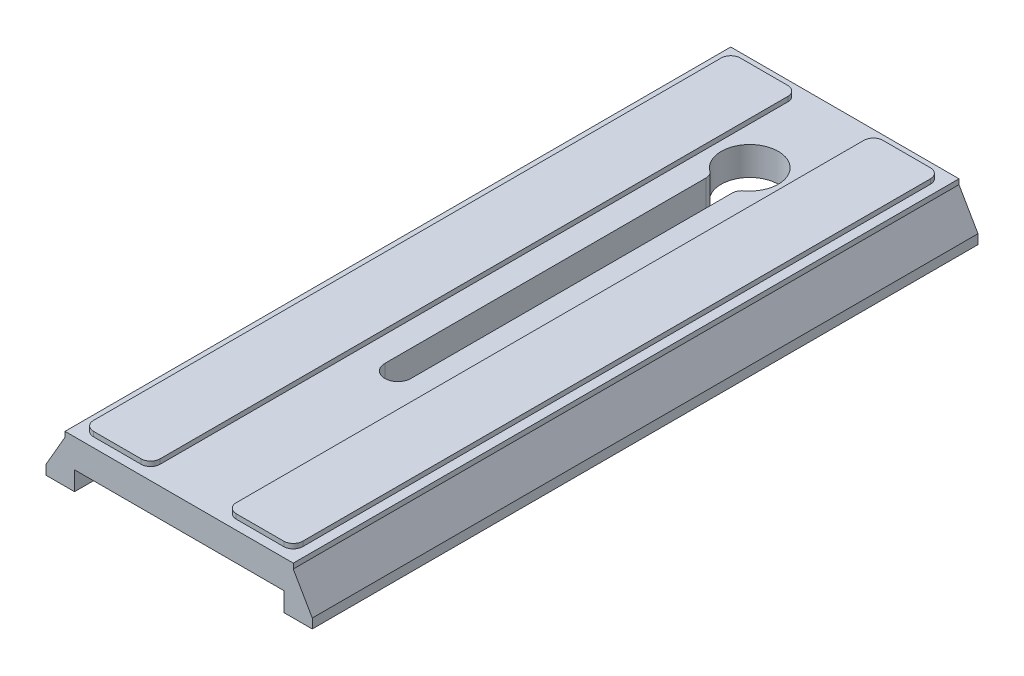
SolidWorks part; units mm, degrees
ref_plane "Спереди" through (0, 0, 0) normal (0, 0, 1) x (1, 0, 0)
ref_plane "Сверху" through (0, 0, 0) normal (0, 1, 0) x (1, 0, 0)
ref_plane "Справа" through (0, 0, 0) normal (1, 0, 0) x (0, 0, -1)
sketch "Эскиз1" plane through (0, 0, 0) normal (0, 0, 1) x (1, 0, 0)
  line L0 (-28, 0) -> (28, 0)
  line L1 (28, 0) -> (28, 2)
  line L2 (28, 2) -> (24, 8.9282)
  line L3 (24, 8.9282) -> (24, 10)
  line L4 (24, 10) -> (-24, 10)
  line L5 (-24, 10) -> (-24, 8.9282)
  line L6 (-24, 8.9282) -> (-28, 2)
  line L7 (-28, 2) -> (-28, 0)
  line L8 (0, 40.7669) -> (0, -10.3588) construction
  point P7 (0, 0)
  point P12 (0, 10)
  dimension "D1" = 56
  dimension "D2" = 48
  dimension "D3" = 2
  dimension "D4" = 2
  dimension "D5" = 10
  dimension "D6" = 60
  dimension "D7" = 60
extrude "Бобышка-Вытянуть1" add sketch "Эскиз1" along normal blind 140
sketch "Эскиз2" plane through (0, 0, 0) normal (0, -1, 0) x (1, 0, 0)
  line L0 (0, 140) -> (0, 0) construction
  line L1 (-28, 140) -> (28, 140) construction
  line L2 (-28, 0) -> (28, 0) construction
  line L3 (-22, 140) -> (-22, 131)
  line L4 (-22, 131) -> (-17, 116)
  line L5 (-17, 116) -> (-17, 112)
  line L6 (-17, 112) -> (-21, 112)
  line L7 (-21, 112) -> (-21, 28)
  line L8 (-28, 70) -> (28, 70) construction
  line L9 (-28, 140) -> (-28, 0) construction
  line L10 (28, 140) -> (28, 0) construction
  line L11 (-17, 28) -> (-21, 28)
  line L12 (-17, 24) -> (-17, 28)
  line L13 (-22, 9) -> (-17, 24)
  line L14 (-22, 0) -> (-22, 9)
  line L15 (22, 0) -> (22, 9)
  line L16 (22, 9) -> (17, 24)
  line L17 (17, 24) -> (17, 28)
  line L18 (17, 28) -> (21, 28)
  line L19 (21, 112) -> (21, 28)
  line L20 (17, 112) -> (21, 112)
  line L21 (17, 116) -> (17, 112)
  line L22 (22, 131) -> (17, 116)
  line L23 (22, 140) -> (22, 131)
  line L24 (-22, 140) -> (22, 140)
  line L25 (-22, 0) -> (22, 0)
  point P19 (-21, 70)
  dimension "D1" = 7
  dimension "D2" = 11
  dimension "D3" = 9
  dimension "D4" = 4
  dimension "D5" = 28
  dimension "D6" = 6
extrude "Вырез-Вытянуть1" cut sketch "Эскиз2" against normal blind 4
sketch "Эскиз3" plane through (0, 10, 0) normal (0, 1, 0) x (1, 0, 0)
  line L0 (0, 0) -> (0, -140) construction
  line L1 (24, 0) -> (-24, 0) construction
  line L2 (24, -140) -> (-24, -140) construction
  line L3 (0, -20) -> (0, -94) construction
  line L4 (2.75, -20) -> (2.75, -94)
  line L5 (-2.75, -20) -> (-2.75, -94)
  arc A0 (2.75, -20) -> (-2.75, -20) centre (0, -20) ccw
  arc A1 (-2.75, -94) -> (2.75, -94) centre (0, -94) ccw
  point P8 (0, -57)
  dimension "D1" = 2.75
  dimension "D2" = 46
  dimension "D3" = 20
extrude "Вырез-Вытянуть2" cut sketch "Эскиз3" against normal through all
sketch "Эскиз4" plane through (0, 10, 0) normal (0, 1, 0) x (1, 0, 0)
  line L0 (0, 0) -> (0, -140) construction
  line L1 (24, 0) -> (-24, 0) construction
  line L2 (24, -140) -> (-24, -140) construction
  circle A0 centre (0, -20) radius 6
  dimension "D1" = 12
  dimension "D2" = 20
extrude "Вырез-Вытянуть3" cut sketch "Эскиз4" against normal through all
sketch "Эскиз5" plane through (0, 10, 0) normal (0, 1, 0) x (1, 0, 0)
  line L0 (0, 0) -> (0, -140) construction
  line L1 (24, -140) -> (-24, -140) construction
  line L2 (-15, 0) -> (-15, -140) construction
  line L3 (24, 0) -> (-24, 0) construction
  line L4 (-24, -70) -> (24, -70) construction
  line L5 (-24, -140) -> (-24, 0) construction
  line L6 (24, -140) -> (24, 0) construction
  line L7 (22, -138) -> (8, -138)
  line L8 (-22, -2) -> (-8, -2)
  line L9 (-22, -2) -> (-22, -138)
  line L10 (-22, -138) -> (-8, -138)
  line L11 (-8, -2) -> (-8, -138)
  line L12 (-22, -2) -> (-8, -138) construction
  line L13 (-22, -138) -> (-8, -2) construction
  line L14 (8, -2) -> (8, -138)
  line L15 (22, -2) -> (8, -2)
  line L16 (22, -2) -> (22, -138)
  point P15 (-15, -70)
  dimension "D1" = 9
  dimension "D2" = 2
  dimension "D3" = 2
extrude "Бобышка-Вытянуть2" add sketch "Эскиз5" along normal blind 1
fillet "Скругление1" radius 2 10 edges at (8, 10.5, 2) (-22, 10.5, 2) (22, 10.5, 2) (-8, 10.5, 2) (-2.75, 7, 25.3327) (2.75, 7, 25.3327) (22, 10.5, 138) (8, 10.5, 138) (-8, 10.5, 138) (-22, 10.5, 138)
